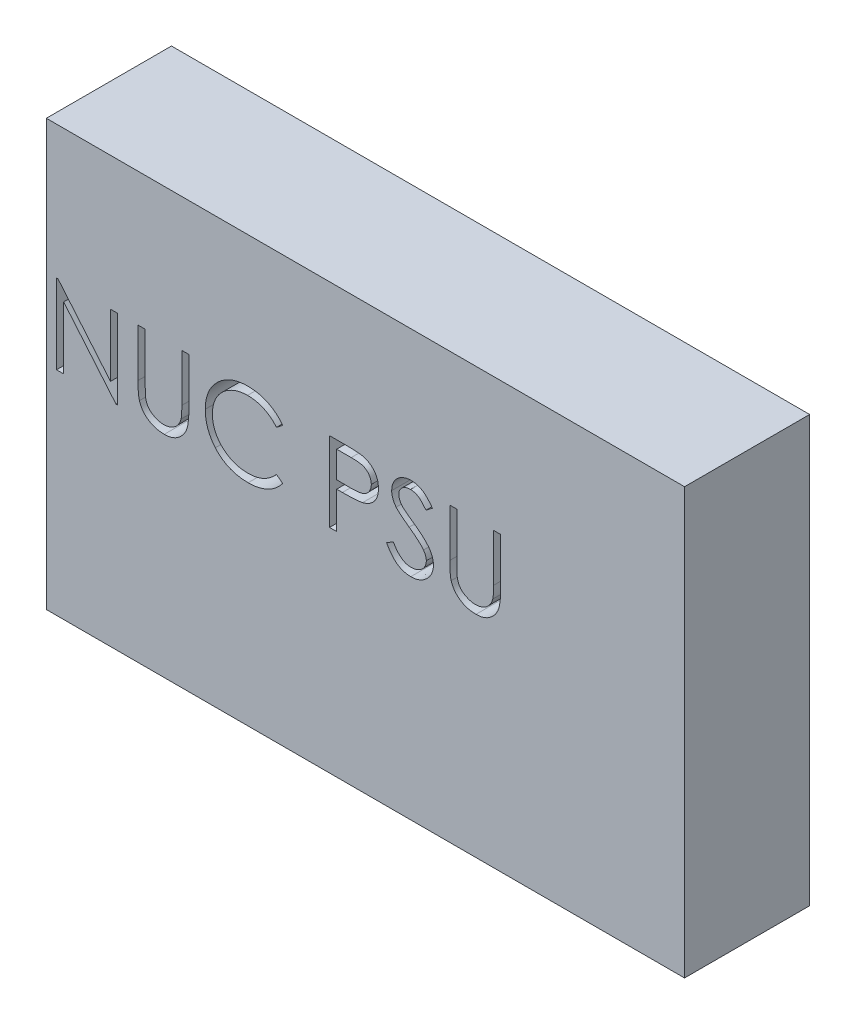
SolidWorks part; units mm, degrees
ref_plane "Front Plane" through (0, 0, 0) normal (0, 0, 1) x (1, 0, 0)
ref_plane "Top Plane" through (0, 0, 0) normal (0, 1, 0) x (1, 0, 0)
ref_plane "Right Plane" through (0, 0, 0) normal (1, 0, 0) x (0, 0, -1)
sketch "Sketch1" plane through (0, 0, 0) normal (0, 0, 1) x (1, 0, 0)
  line L1 (-51, 34) -> (51, 34)
  line L2 (-51, 34) -> (-51, -34)
  line L3 (-51, -34) -> (51, -34)
  line L4 (51, 34) -> (51, -34)
  line L5 (-51, 34) -> (51, -34) construction
  line L6 (-51, -34) -> (51, 34) construction
  point P0 (0, 0)
  dimension "D1" = 102
  dimension "D2" = 68
extrude "Boss-Extrude1" add sketch "Sketch1" along normal blind 20
sketch "Sketch2" plane through (0, 0, 20) normal (0, 0, 1) x (1, 0, 0)
  line L0 (-51, 0) -> (51, 0) construction
  line L1 (-51, 34) -> (-51, -34) construction
  line L2 (51, -34) -> (51, 34) construction
  text T0 "NUC PSU" font "Century Gothic" height 12.7
extrude "Cut-Extrude1" cut sketch "Sketch2" against normal through all both and the other way through all
